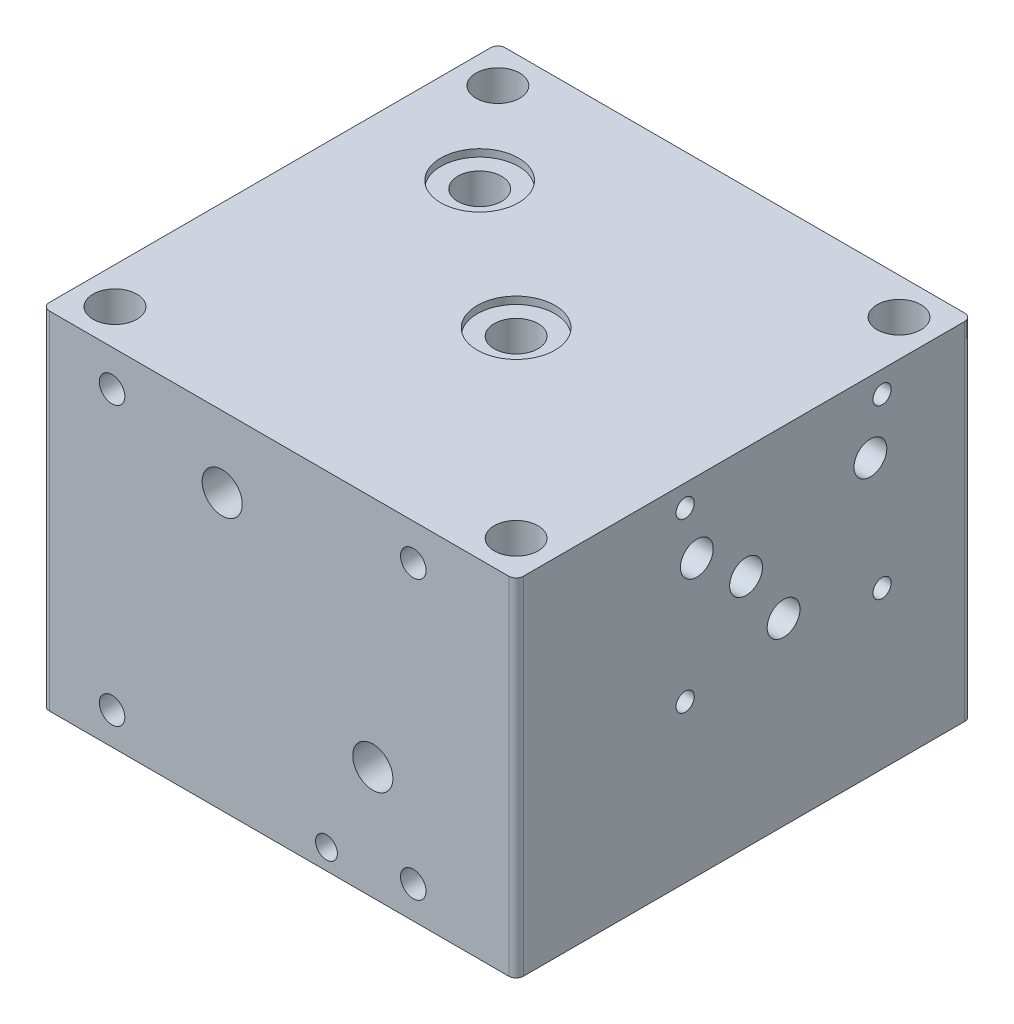
SolidWorks part; units mm, degrees
ref_plane "Front" through (0, 0, 0) normal (0, 0, 1) x (1, 0, 0)
ref_plane "Top" through (0, 0, 0) normal (0, 1, 0) x (1, 0, 0)
ref_plane "Right" through (0, 0, 0) normal (1, 0, 0) x (0, 0, -1)
sketch "草图1" plane through (0, 0, 0) normal (0, 1, 0) x (1, 0, 0)
  line L1 (-65, 62.5) -> (65, 62.5)
  line L2 (-65, 62.5) -> (-65, -62.5)
  line L3 (-65, -62.5) -> (65, -62.5)
  line L4 (65, 62.5) -> (65, -62.5)
  line L5 (-65, 62.5) -> (65, -62.5) construction
  line L6 (-65, -62.5) -> (65, 62.5) construction
  point P0 (0, 0)
  dimension "D1" = 125
  dimension "D2" = 130
extrude "凸台-拉伸1" add sketch "草图1" along normal blind 100
fillet "圆角1" radius 2 4 edges at (-65, 50, 62.5) (-65, 50, -62.5) (65, 50, -62.5) (65, 50, 62.5)
sketch "草图2" plane through (0, 100, 0) normal (0, 1, 0) x (1, 0, 0)
  line L1 (-55, 52.5) -> (55, 52.5) construction
  line L2 (-55, 52.5) -> (-55, -52.5) construction
  line L3 (-55, -52.5) -> (55, -52.5) construction
  line L4 (55, 52.5) -> (55, -52.5) construction
  line L5 (-55, 52.5) -> (55, -52.5) construction
  line L6 (-55, -52.5) -> (55, 52.5) construction
  circle A0 centre (55, 52.5) radius 6
  circle A1 centre (55, -52.5) radius 6
  circle A2 centre (-55, 52.5) radius 6
  circle A3 centre (-55, -52.5) radius 6
  point P0 (0, 0)
  dimension "D3" = 12
  dimension "D4" = 12
  dimension "D5" = 12
  dimension "D6" = 12
  dimension "D1" = 105
  dimension "D2" = 110
extrude "切除-拉伸1" cut sketch "草图2" against normal through all
sketch "草图3" plane through (0, 100, 0) normal (0, 1, 0) x (1, 0, 0)
  line L0 (-65, 60.5) -> (-65, -60.5) construction
  line L1 (-63, -62.5) -> (63, -62.5) construction
  circle A0 centre (-35, 27.5) radius 6
  circle A1 centre (5, -2.5) radius 6
  dimension "D1" = 12
  dimension "D2" = 30
  dimension "D3" = 70
  dimension "D4" = 90
  dimension "D5" = 60
extrude "切除-拉伸2" cut sketch "草图3" against normal through all
sketch "草图6" plane through (0, 100, 0) normal (0, 1, 0) x (1, 0, 0)
  circle A0 centre (5, -2.5) radius 11.5
  circle A1 centre (-35, 27.5) radius 11.5
  dimension "D1" = 23
  dimension "D2" = 23
extrude "切除-拉伸3" cut sketch "草图6" against normal blind 2
sketch "草图7" plane through (-65, 0, 0) normal (-1, 0, 0) x (0, 0, 1)
  line L1 (-62.5, 0) -> (-62.5, 100) construction
  line L2 (-21.5, 57) -> (32.5, 57) construction
  line L3 (-21.5, 57) -> (-21.5, 12) construction
  line L4 (-21.5, 12) -> (32.5, 12) construction
  line L5 (32.5, 57) -> (32.5, 12) construction
  line L6 (-60.5, 0) -> (60.5, 0) construction
  circle A0 centre (5.5, 50.7) radius 4.5
  circle A1 centre (15.8, 35.6) radius 4.5
  circle A2 centre (-4.8, 35.6) radius 4.5
  circle A3 centre (29.3, 24.5) radius 4.5
  circle A4 centre (-18.3, 24.5) radius 4.5
  dimension "D1" = 9
  dimension "D2" = 54
  dimension "D4" = 27
  dimension "D5" = 6.3
  dimension "D6" = 16.7
  dimension "D7" = 21.4
  dimension "D8" = 37.3
  dimension "D9" = 68
  dimension "D10" = 32.5
  dimension "D11" = 3.2
  dimension "D12" = 50.8
  dimension "D3" = 45
  dimension "D13" = 12
hole_wizard "大小mm 暗销孔8" positions "草图8" profile "草图9" hole size "Ø1.0" standard "GB"
sketch "草图8" plane through (-65, 0, 0) normal (-1, 0, 0) x (0, 0, 1)
  point P0 (5.5, 50.7)
sketch "草图9" plane through (-65, 50.7, 5.5) normal (0, 1, 0) x (0, 0, 1)
  line L0 (0, 0) -> (0, 70.7039)
  line L1 (0, 70.7039) -> (4.5, 68)
  line L2 (4.5, 68) -> (4.5, 0)
  line L5 (4.5, 0) -> (0, 0)
  line L10 (0, 70.7039) -> (-4.5, 68) construction
  line L11 (0, -6.35) -> (0, 107.95) construction
  dimension "孔直径" = 9
  dimension "孔深度" = 68
  dimension "导头角度" = 118
hole_wizard "大小mm 暗销孔8" positions "草图10" profile "草图11" hole size "Ø1.0" standard "GB"
sketch "草图10" plane through (-65, 0, 0) normal (-1, 0, 0) x (0, 0, 1)
  point P0 (-18.3, 24.5)
  point P3 (29.3, 24.5)
sketch "草图11" plane through (-65, 24.5, -18.3) normal (0, 1, 0) x (0, 0, 1)
  line L0 (0, 0) -> (0, 37.7039)
  line L1 (0, 37.7039) -> (4.5, 35)
  line L2 (4.5, 35) -> (4.5, 0)
  line L5 (4.5, 0) -> (0, 0)
  line L10 (0, 37.7039) -> (-4.5, 35) construction
  line L11 (0, -6.35) -> (0, 107.95) construction
  dimension "孔直径" = 9
  dimension "孔深度" = 35
  dimension "导头角度" = 118
sketch "草图12" plane through (0, 0, -62.5) normal (0, 0, -1) x (-1, 0, 0)
  circle A0 centre (34.8378, 24.5) radius 3
  dimension "D1" = 6
hole_wizard "大小mm 暗销孔11" positions "草图13" profile "草图14" hole size "Ø1.0" standard "GB"
sketch "草图13" plane through (0, 0, -62.5) normal (0, 0, -1) x (-1, 0, 0)
  point P0 (34.8378, 24.5)
sketch "草图14" plane through (-34.8378, 24.5, -62.5) normal (1, 0, 0) x (0, 1, 0)
  line L0 (0, 0) -> (0, 92.4034)
  line L1 (0, 92.4034) -> (4, 90)
  line L2 (4, 90) -> (4, 0)
  line L5 (4, 0) -> (0, 0)
  line L10 (0, 92.4034) -> (-4, 90) construction
  line L11 (0, -6.35) -> (0, 107.95) construction
  dimension "孔直径" = 8
  dimension "孔深度" = 90
  dimension "导头角度" = 118
hole_wizard "大小mm 暗销孔8" positions "草图20" profile "草图21" hole size "Ø1.0" standard "GB"
sketch "草图20" plane through (-65, 0, 0) normal (-1, 0, 0) x (0, 0, 1)
  point P0 (15.8, 35.6)
sketch "草图21" plane through (-65, 35.6, 15.8) normal (0, 1, 0) x (0, 0, 1)
  line L0 (0, 0) -> (0, 90.7039)
  line L1 (0, 90.7039) -> (4.5, 88)
  line L2 (4.5, 88) -> (4.5, 0)
  line L5 (4.5, 0) -> (0, 0)
  line L10 (0, 90.7039) -> (-4.5, 88) construction
  line L11 (0, -6.35) -> (0, 107.95) construction
  dimension "孔直径" = 9
  dimension "孔深度" = 88
  dimension "导头角度" = 118
sketch "草图22" plane through (0, 0, 62.5) normal (0, 0, 1) x (1, 0, 0)
  line L1 (-45.7961, 84.0238) -> (36.8039, 84.0238) construction
  line L2 (-45.7961, 84.0238) -> (-45.7961, 7.8238) construction
  line L3 (-45.7961, 7.8238) -> (36.8039, 7.8238) construction
  line L4 (36.8039, 84.0238) -> (36.8039, 7.8238) construction
  circle A0 centre (25.7039, 30.0238) radius 4.5
  circle A1 centre (-15.5961, 74.5238) radius 4.5
  circle A2 centre (13.0039, 4.6238) radius 3
  dimension "D3" = 54
  dimension "D4" = 11.1
  dimension "D5" = 9.5
  dimension "D6" = 52.4
  dimension "D7" = 6
  dimension "D8" = 9
  dimension "D9" = 79.4
  dimension "D10" = 23.8
  dimension "D1" = 82.6
  dimension "D2" = 76.2
hole_wizard "大小mm 暗销孔8" positions "草图24" profile "草图25" hole size "Ø1.0" standard "GB"
sketch "草图24" plane through (0, 0, 62.5) normal (0, 0, 1) x (1, 0, 0)
  point P0 (25.7039, 30.0238)
sketch "草图25" plane through (25.7039, 30.0238, 62.5) normal (1, 0, 0) x (0, -1, 0)
  line L0 (0, 0) -> (0, 53.3047)
  line L1 (0, 53.3047) -> (5.5, 50)
  line L2 (5.5, 50) -> (5.5, 0)
  line L5 (5.5, 0) -> (0, 0)
  line L10 (0, 53.3047) -> (-5.5, 50) construction
  line L11 (0, -6.35) -> (0, 107.95) construction
  dimension "孔直径" = 11
  dimension "孔深度" = 50
  dimension "导头角度" = 118
sketch "草图26" plane through (65, 0, 0) normal (1, 0, 0) x (0, 0, -1)
  line L1 (-16.1505, 134.0238) -> (37.8495, 134.0238) construction
  line L2 (-16.1505, 134.0238) -> (-16.1505, 42.0238) construction
  line L3 (-16.1505, 88.0238) -> (37.8495, 88.0238) construction
  line L4 (37.8495, 134.0238) -> (37.8495, 42.0238) construction
  line L6 (-16.1505, 42.0238) -> (37.8495, 42.0238) construction
  line L7 (-62.5, 79.0238) -> (-62.5, 70.0238) construction
  line L8 (-62.5, 74.5238) -> (75.2847, 74.5238) construction
  circle A0 centre (10.8495, 127.7238) radius 4.5
  circle A1 centre (0.5495, 112.6238) radius 4.5
  circle A2 centre (34.6495, 74.5238) radius 4.5
  circle A3 centre (-12.9505, 101.5238) radius 4.5
  circle A4 centre (34.6495, 101.5238) radius 4.5
  circle A5 centre (-12.9505, 74.5238) radius 4.5
  circle A6 centre (0.5495, 63.4238) radius 4.5
  circle A7 centre (10.8495, 48.3238) radius 4.5
  dimension "D3" = 27
  dimension "D4" = 6.3
  dimension "D5" = 16.7
  dimension "D6" = 21.4
  dimension "D7" = 3.2
  dimension "D8" = 32.5
  dimension "D9" = 9
  dimension "D10" = 50.8
  dimension "D1" = 54
  dimension "D2" = 46
hole_wizard "大小mm 暗销孔14" positions "草图27" profile "草图28" hole size "Ø1.0" standard "GB"
sketch "草图27" plane through (0, 0, 62.5) normal (0, 0, 1) x (1, 0, 0)
  point P0 (-15.5961, 74.5238)
sketch "草图28" plane through (-15.5961, 74.5238, 62.5) normal (1, 0, 0) x (0, -1, 0)
  line L0 (0, 0) -> (0, 96.3047)
  line L1 (0, 96.3047) -> (5.5, 93)
  line L2 (5.5, 93) -> (5.5, 0)
  line L5 (5.5, 0) -> (0, 0)
  line L10 (0, 96.3047) -> (-5.5, 93) construction
  line L11 (0, -6.35) -> (0, 107.95) construction
  dimension "孔直径" = 11
  dimension "孔深度" = 93
  dimension "导头角度" = 118
hole_wizard "大小mm 暗销孔8" positions "草图29" profile "草图30" hole size "Ø1.0" standard "GB"
sketch "草图29" plane through (65, 0, 0) normal (1, 0, 0) x (0, 0, -1)
  point P0 (-12.9505, 74.5238)
  point P3 (34.6495, 74.5238)
sketch "草图30" plane through (65, 74.5238, 12.9505) normal (0, 1, 0) x (0, 0, -1)
  line L0 (0, 0) -> (0, 87.7039)
  line L1 (0, 87.7039) -> (4.5, 85)
  line L2 (4.5, 85) -> (4.5, 0)
  line L5 (4.5, 0) -> (0, 0)
  line L10 (0, 87.7039) -> (-4.5, 85) construction
  line L11 (0, -6.35) -> (0, 107.95) construction
  dimension "孔直径" = 9
  dimension "孔深度" = 85
  dimension "导头角度" = 118
hole_wizard "大小mm 暗销孔10" positions "草图32" profile "草图33" hole size "Ø1.0" standard "GB"
sketch "草图32" plane through (65, 0, 0) normal (1, 0, 0) x (0, 0, -1)
  point P0 (10.8495, 48.3238)
sketch "草图33" plane through (65, 48.3238, -10.8495) normal (0, 1, 0) x (0, 0, -1)
  line L0 (0, 0) -> (0, 82.7039)
  line L1 (0, 82.7039) -> (4.5, 80)
  line L2 (4.5, 80) -> (4.5, 0)
  line L5 (4.5, 0) -> (0, 0)
  line L10 (0, 82.7039) -> (-4.5, 80) construction
  line L11 (0, -6.35) -> (0, 107.95) construction
  dimension "孔直径" = 9
  dimension "孔深度" = 80
  dimension "导头角度" = 118
hole_wizard "大小mm 暗销孔10" positions "草图34" profile "草图35" hole size "Ø1.0" standard "GB"
sketch "草图34" plane through (-65, 0, 0) normal (-1, 0, 0) x (0, 0, 1)
  point P0 (-4.8, 35.6)
sketch "草图35" plane through (-65, 35.6, -4.8) normal (0, 1, 0) x (0, 0, 1)
  line L0 (0, 0) -> (0, 57.7039)
  line L1 (0, 57.7039) -> (4.5, 55)
  line L2 (4.5, 55) -> (4.5, 0)
  line L5 (4.5, 0) -> (0, 0)
  line L10 (0, 57.7039) -> (-4.5, 55) construction
  line L11 (0, -6.35) -> (0, 107.95) construction
  dimension "孔直径" = 9
  dimension "孔深度" = 55
  dimension "导头角度" = 118
sketch "草图36" plane through (0, 0, -62.5) normal (0, 0, -1) x (-1, 0, 0)
  circle A0 centre (13.3271, 41.8211) radius 4.5
  dimension "D1" = 9
hole_wizard "大小mm 暗销孔11" positions "草图37" profile "草图38" hole size "Ø1.0" standard "GB"
sketch "草图37" plane through (0, 0, -62.5) normal (0, 0, -1) x (-1, 0, 0)
  point P0 (13.3271, 41.8211)
sketch "草图38" plane through (-13.3271, 41.8211, -62.5) normal (1, 0, 0) x (0, 1, 0)
  line L0 (0, 0) -> (0, 62.4034)
  line L1 (0, 62.4034) -> (4, 60)
  line L2 (4, 60) -> (4, 0)
  line L5 (4, 0) -> (0, 0)
  line L10 (0, 62.4034) -> (-4, 60) construction
  line L11 (0, -6.35) -> (0, 107.95) construction
  dimension "孔直径" = 8
  dimension "孔深度" = 60
  dimension "导头角度" = 118
hole_wizard "大小mm 暗销孔12" positions "草图39" profile "草图40" hole size "Ø1.0" standard "GB"
sketch "草图39" plane through (65, 0, 0) normal (1, 0, 0) x (0, 0, -1)
  point P0 (0.5495, 63.4238)
sketch "草图40" plane through (65, 63.4238, -0.5495) normal (0, 1, 0) x (0, 0, -1)
  line L0 (0, 0) -> (0, 40.7039)
  line L1 (0, 40.7039) -> (4.5, 38)
  line L2 (4.5, 38) -> (4.5, 0)
  line L5 (4.5, 0) -> (0, 0)
  line L10 (0, 40.7039) -> (-4.5, 38) construction
  line L11 (0, -6.35) -> (0, 107.95) construction
  dimension "孔直径" = 9
  dimension "孔深度" = 38
  dimension "导头角度" = 118
sketch "草图41" plane through (0, 0, -62.5) normal (0, 0, -1) x (-1, 0, 0)
  circle A0 centre (-31.9192, 63.2142) radius 4
  dimension "D1" = 8
hole_wizard "大小mm 暗销孔13" positions "草图42" profile "草图43" hole size "Ø1.0" standard "GB"
sketch "草图42" plane through (0, 0, -62.5) normal (0, 0, -1) x (-1, 0, 0)
  point P0 (-31.9192, 63.2142)
sketch "草图43" plane through (31.9192, 63.2142, -62.5) normal (1, 0, 0) x (0, 1, 0)
  line L0 (0, 0) -> (0, 57.4554)
  line L1 (0, 57.4554) -> (4, 57.4554)
  line L2 (4, 57.4554) -> (4, 0)
  line L5 (4, 0) -> (0, 0)
  line L11 (0, -6.35) -> (0, 107.95) construction
  dimension "通孔孔直径" = 8
  dimension "通孔孔深度" = 57.4554
hole_wizard "M10x1.0 螺纹孔1" positions "草图16" profile "草图15" tap size "M10x1.0" standard "GB"
sketch "草图16" plane through (0, 0, -62.5) normal (0, 0, -1) x (-1, 0, 0)
  point P0 (34.8378, 24.5)
  point P4 (13.3271, 41.8211)
  point P8 (-31.9192, 63.2142)
sketch "草图15" plane through (-34.8378, 24.5, -62.5) normal (1, 0, 0) x (0, 1, 0)
  line L0 (0, 0) -> (0, 12.7039)
  line L1 (0, 12.7039) -> (4.5, 10)
  line L2 (4.5, 10) -> (4.5, 0)
  line L5 (4.5, 0) -> (0, 0)
  line L10 (0, 12.7039) -> (-4.5, 10) construction
  line L11 (0, -6.35) -> (0, 107.95) construction
  dimension "螺纹孔钻头直径" = 9
  dimension "螺纹孔钻头深度" = 10
  dimension "导头角度" = 118
cosmetic thread "孔螺蚊线4" parameters "D1"=8, "D2"=10
cosmetic thread "孔螺蚊线5" parameters "D1"=8, "D2"=10
cosmetic thread "孔螺蚊线7" parameters "D1"=8, "D2"=10
hole_wizard "大小mm 暗销孔14" positions "草图44" profile "草图45" hole size "Ø1.0" standard "GB"
sketch "草图44" plane through (0, 0, 62.5) normal (0, 0, 1) x (1, 0, 0)
  point P3 (13.0039, 4.6238)
sketch "草图45" plane through (13.0039, 4.6238, 62.5) normal (1, 0, 0) x (0, -1, 0)
  line L0 (0, 0) -> (0, 13.8026)
  line L1 (0, 13.8026) -> (3, 12)
  line L2 (3, 12) -> (3, 0)
  line L5 (3, 0) -> (0, 0)
  line L10 (0, 13.8026) -> (-3, 12) construction
  line L11 (0, -6.35) -> (0, 107.95) construction
  dimension "孔直径" = 6
  dimension "孔深度" = 12
  dimension "导头角度" = 118
sketch "草图46" plane through (0, 0, 0) normal (0, -1, 0) x (1, 0, 0)
  line L4 (63, 62.5) -> (-63, 62.5)
  line L5 (-65, 60.5) -> (-65, -60.5)
  line L6 (-63, -62.5) -> (63, -62.5)
  line L7 (65, -60.5) -> (65, 60.5)
  line L8 (63, 62.5) -> (-63, 62.5)
  line L9 (-65, 60.5) -> (-65, -60.5)
  line L10 (-63, -62.5) -> (63, -62.5)
  line L11 (65, -60.5) -> (65, 60.5)
  circle A0 centre (5, 2.5) radius 6 construction
  circle A1 centre (-35, -27.5) radius 6 construction
  circle A2 centre (-55, -52.5) radius 6 construction
  circle A3 centre (55, -52.5) radius 6 construction
  arc A4 (-63, 62.5) -> (-65, 60.5) centre (-63, 60.5) ccw
  arc A5 (-65, -60.5) -> (-63, -62.5) centre (-63, -60.5) ccw
  arc A6 (63, -62.5) -> (65, -60.5) centre (63, -60.5) ccw
  arc A7 (65, 60.5) -> (63, 62.5) centre (63, 60.5) ccw
  arc A8 (-63, 62.5) -> (-65, 60.5) centre (-63, 60.5) ccw
  arc A9 (-65, -60.5) -> (-63, -62.5) centre (-63, -60.5) ccw
  arc A10 (63, -62.5) -> (65, -60.5) centre (63, -60.5) ccw
  arc A11 (65, 60.5) -> (63, 62.5) centre (63, 60.5) ccw
  circle A12 centre (55, 52.5) radius 6 construction
  circle A13 centre (-55, 52.5) radius 6 construction
  circle A14 centre (5, 2.5) radius 6
  circle A15 centre (-35, -27.5) radius 6
  circle A16 centre (-55, -52.5) radius 6
  circle A17 centre (55, -52.5) radius 6
  circle A18 centre (55, 52.5) radius 6
  circle A19 centre (-55, 52.5) radius 6
  dimension "D1" = 0
extrude "凸台-拉伸2" add sketch "草图46" along normal blind 1
sketch "草图47" plane through (0, 0, 62.5) normal (0, 0, 1) x (1, 0, 0)
  line L0 (65, 100) -> (65, -1) construction
  line L1 (-65, 100) -> (65, 100)
  line L2 (-65, 100) -> (-65, 94)
  line L3 (-65, 94) -> (65, 94)
  line L4 (65, 100) -> (65, 94)
  dimension "D1" = 6
extrude "切除-拉伸4" cut sketch "草图47" against normal through all
sketch "草图48" plane through (0, 94, 0) normal (0, 1, 0) x (1, 0, 0)
  circle A0 centre (5, -2.5) radius 10.65
  circle A1 centre (-35, 27.5) radius 10.65
  dimension "D1" = 21.3
  dimension "D2" = 21.3
extrude "切除-拉伸5" cut sketch "草图48" against normal blind 2
hole_wizard "M6 螺纹孔1" positions "草图49" profile "草图50" tap size "M6" standard "GB"
sketch "草图49" plane through (-65, 0, 0) normal (-1, 0, 0) x (0, 0, 1)
  point P0 (32.5, 57)
  point P3 (32.5, 12)
  point P6 (-21.5, 12)
  point P9 (-21.5, 57)
sketch "草图50" plane through (-65, 57, 32.5) normal (0, 1, 0) x (0, 0, 1)
  line L0 (0, 0) -> (0, 11.5022)
  line L1 (0, 11.5022) -> (2.5, 10)
  line L2 (2.5, 10) -> (2.5, 0)
  line L5 (2.5, 0) -> (0, 0)
  line L10 (0, 11.5022) -> (-2.5, 10) construction
  line L11 (0, -6.35) -> (0, 107.95) construction
  dimension "螺纹孔钻头直径" = 5
  dimension "螺纹孔钻头深度" = 10
  dimension "导头角度" = 118
cosmetic thread "孔螺蚊线8" parameters "D1"=8, "D2"=6
cosmetic thread "孔螺蚊线9" parameters "D1"=8, "D2"=6
cosmetic thread "孔螺蚊线10" parameters "D1"=8, "D2"=6
cosmetic thread "孔螺蚊线11" parameters "D1"=8, "D2"=6
hole_wizard "M6 螺纹孔2" positions "草图51" profile "草图52" tap size "M6" standard "GB"
sketch "草图51" plane through (65, 0, 0) normal (1, 0, 0) x (0, 0, -1)
  point P0 (37.8495, 88.0238)
  point P3 (-16.1505, 88.0238)
  point P6 (-16.1505, 42.0238)
  point P9 (37.8495, 42.0238)
sketch "草图52" plane through (65, 88.0238, -37.8495) normal (0, 1, 0) x (0, 0, -1)
  line L0 (0, 0) -> (0, 11.5022)
  line L1 (0, 11.5022) -> (2.5, 10)
  line L2 (2.5, 10) -> (2.5, 0)
  line L5 (2.5, 0) -> (0, 0)
  line L10 (0, 11.5022) -> (-2.5, 10) construction
  line L11 (0, -6.35) -> (0, 107.95) construction
  dimension "螺纹孔钻头直径" = 5
  dimension "螺纹孔钻头深度" = 10
  dimension "导头角度" = 118
cosmetic thread "孔螺蚊线12" parameters "D1"=8, "D2"=6
cosmetic thread "孔螺蚊线13" parameters "D1"=8, "D2"=6
cosmetic thread "孔螺蚊线14" parameters "D1"=8, "D2"=6
cosmetic thread "孔螺蚊线15" parameters "D1"=8, "D2"=6
hole_wizard "M8x1.0 螺纹孔1" positions "草图53" profile "草图54" tap size "M8x1.0" standard "GB"
sketch "草图53" plane through (0, 0, 62.5) normal (0, 0, 1) x (1, 0, 0)
  point P0 (36.8039, 7.8238)
  point P3 (36.8039, 84.0238)
  point P6 (-45.7961, 84.0238)
  point P9 (-45.7961, 7.8238)
sketch "草图54" plane through (36.8039, 7.8238, 62.5) normal (1, 0, 0) x (0, -1, 0)
  line L0 (0, 0) -> (0, 12.103)
  line L1 (0, 12.103) -> (3.5, 10)
  line L2 (3.5, 10) -> (3.5, 0)
  line L5 (3.5, 0) -> (0, 0)
  line L10 (0, 12.103) -> (-3.5, 10) construction
  line L11 (0, -6.35) -> (0, 107.95) construction
  dimension "螺纹孔钻头直径" = 7
  dimension "螺纹孔钻头深度" = 10
  dimension "导头角度" = 118
cosmetic thread "孔螺蚊线16" parameters "D1"=8, "D2"=8
cosmetic thread "孔螺蚊线17" parameters "D1"=8, "D2"=8
cosmetic thread "孔螺蚊线18" parameters "D1"=8, "D2"=8
cosmetic thread "孔螺蚊线19" parameters "D1"=8, "D2"=8
